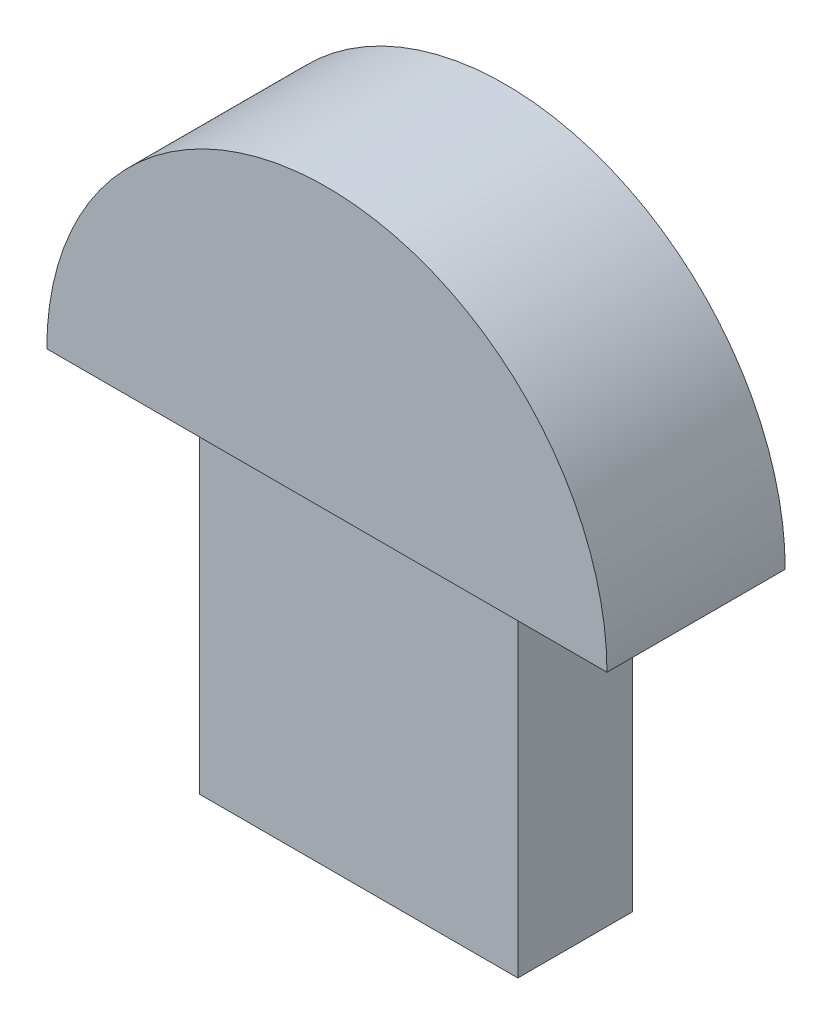
SolidWorks part; units mm, degrees
ref_plane "Front Plane" through (0, 0, 0) normal (0, 0, 1) x (1, 0, 0)
ref_plane "Top Plane" through (0, 0, 0) normal (0, 1, 0) x (1, 0, 0)
ref_plane "Right Plane" through (0, 0, 0) normal (1, 0, 0) x (0, 0, -1)
sketch "Sketch1" plane through (0, 0, 0) normal (0, 1, 0) x (1, 0, 0)
  line L1 (-6.25, 2.25) -> (6.25, 2.25)
  line L2 (-6.25, 2.25) -> (-6.25, -2.25)
  line L3 (-6.25, -2.25) -> (6.25, -2.25)
  line L4 (6.25, 2.25) -> (6.25, -2.25)
  line L5 (-6.25, 2.25) -> (6.25, -2.25) construction
  line L6 (-6.25, -2.25) -> (6.25, 2.25) construction
  point P0 (0, 0)
  dimension "D1" = 12.5
  dimension "D2" = 4.5
extrude "Boss-Extrude1" add sketch "Sketch1" along normal blind 13.4
sketch "Sketch2" plane through (0, 0, 0) normal (0, 0, 1) x (1, 0, 0)
  line L0 (-11, 13.4) -> (11, 13.4)
  line L1 (0, 0) -> (0, 11.176) construction
  line L2 (-6.25, 0) -> (6.25, 0) construction
  arc A0 (-11, 13.4) -> (11, 13.4) centre (0, 13.4) cw
  point P3 (0, 13.4)
  point P4 (0, 0)
  dimension "D1" = 22
extrude "Boss-Extrude2" add sketch "Sketch2" along normal mid plane 7
